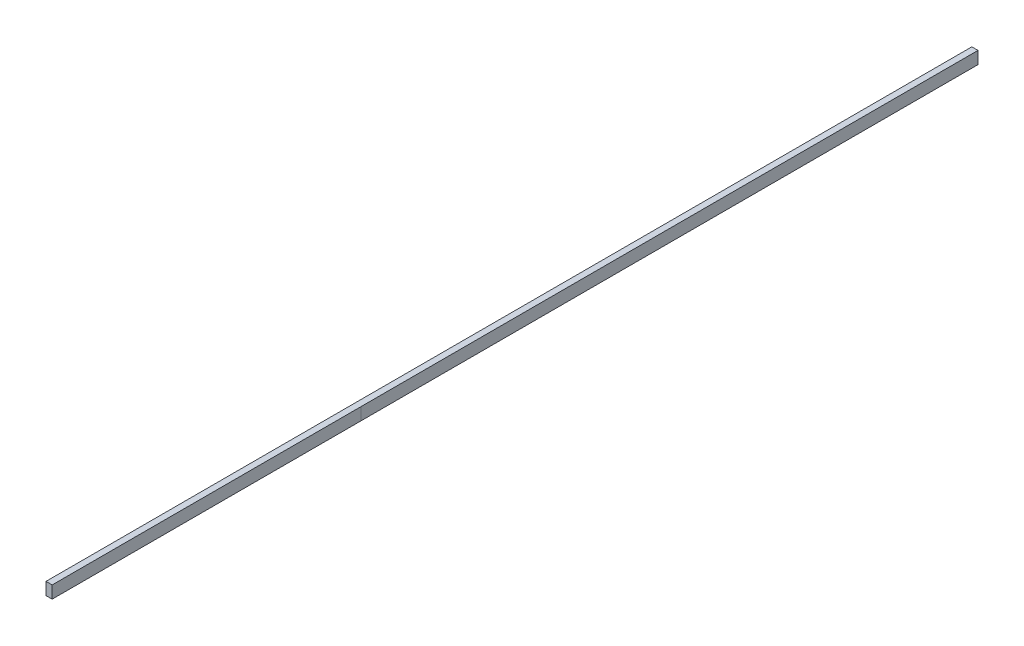
SolidWorks part; units mm, degrees
material "AISI 1020"
ref_plane "Front Plane" through (0, 0, 0) normal (0, 0, 1) x (1, 0, 0)
ref_plane "Top Plane" through (0, 0, 0) normal (0, 1, 0) x (1, 0, 0)
ref_plane "Right Plane" through (0, 0, 0) normal (1, 0, 0) x (0, 0, -1)
sketch "Sketch1" plane through (0, 0, 0) normal (0, 0, 1) x (1, 0, 0)
  line L1 (0, 0) -> (10, 0)
  line L2 (0, 0) -> (0, 20)
  line L3 (0, 20) -> (10, 20)
  line L4 (10, 0) -> (10, 20)
  dimension "D1" = 20
  dimension "D2" = 10
extrude "Boss-Extrude1" add sketch "Sketch1" along normal blind 1500
sketch "Sketch2" plane through (0, 0, 0) normal (-1, 0, 0) x (0, 0, 1)
  line L9 (1000, 20) -> (1000, 0)
split line "Split Line1"
sketch "Sketch3" plane through (0, 0, 0) normal (-1, 0, 0) x (0, 0, 1)
  line L0 (1011.919, 20) -> (1011.919, 0)
  line L1 (1500, 20) -> (1000, 20) construction
  line L2 (5.5, 0) -> (-5.5, 0) construction
  line L3 (1011.919, 0) -> (1000, 0)
  line L4 (1000, 0) -> (1000, 20)
  line L5 (1000, 20) -> (1011.919, 20)
split line "Split Line2"
sketch "Sketch4" plane through (10, 0, 0) normal (1, 0, 0) x (0, 0, -1)
  line L3 (-1000, 20) -> (-1000, 0)
  line L4 (-1500, 20) -> (0, 20) construction
  line L5 (5.5, 0) -> (-5.5, 0) construction
split line "Split Line3"
